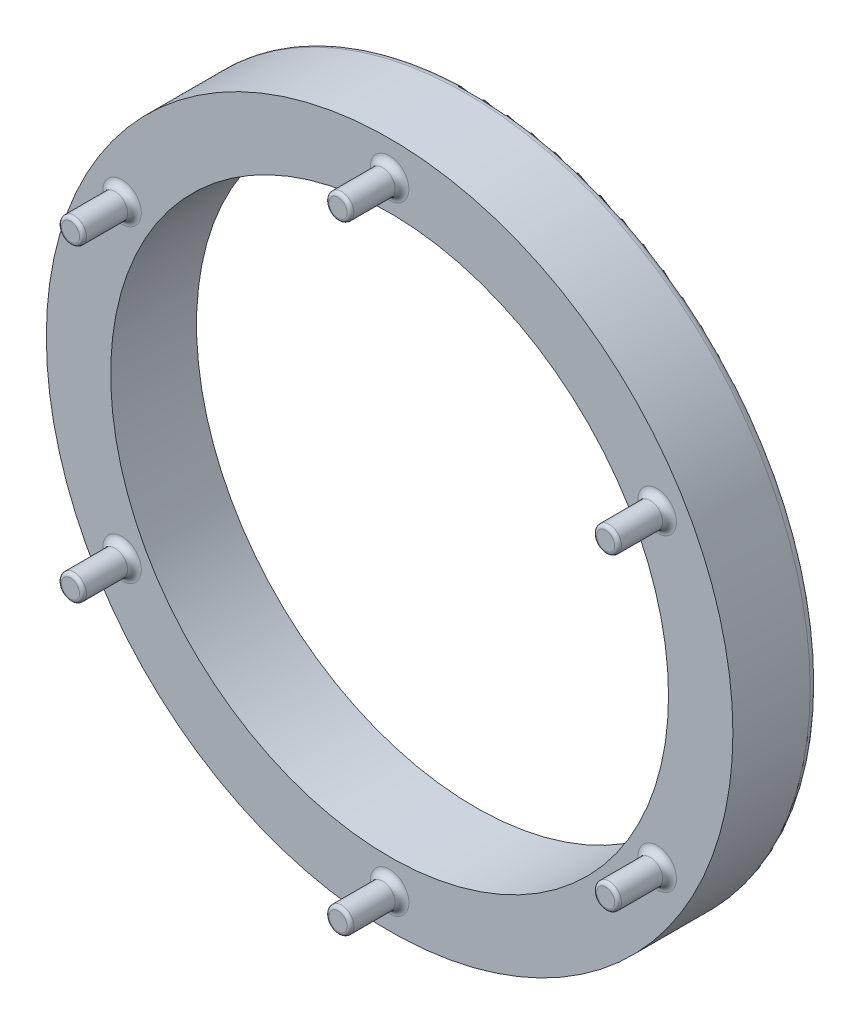
SolidWorks part; units mm, degrees
ref_plane "Front Plane" through (0, 0, 0) normal (0, 0, 1) x (1, 0, 0)
ref_plane "Top Plane" through (0, 0, 0) normal (0, 1, 0) x (1, 0, 0)
ref_plane "Right Plane" through (0, 0, 0) normal (1, 0, 0) x (0, 0, -1)
sketch "Sketch1" plane through (0, 0, 0) normal (0, 0, 1) x (1, 0, 0)
  circle A0 centre (0, 0) radius 20
  dimension "D1" = 40
extrude "Boss-Extrude1" add sketch "Sketch1" along normal blind 5
sketch "Sketch2" plane through (0, 0, 5) normal (0, 0, 1) x (1, 0, 0)
  circle A0 centre (0, 0) radius 18
  dimension "D1" = 36
sketch "Sketch3" plane through (0, 0, 5) normal (0, 0, 1) x (1, 0, 0)
  circle A0 centre (0, 18) radius 0.725
  circle A1 centre (0, 0) radius 18 construction
  circle A2 centre (15.5885, 9) radius 0.725
  circle A3 centre (15.5885, -9) radius 0.725
  circle A4 centre (0, -18) radius 0.725
  circle A5 centre (-15.5885, -9) radius 0.725
  circle A6 centre (-15.5885, 9) radius 0.725
  point P16 (0, 0)
  dimension "D1" = 1.45
  dimension "D2" = 6
extrude "Boss-Extrude3" add sketch "Sketch3" along normal blind 3
fillet "Fillet1" radius 0.4 6 edges at (-14.8635, -9, 5) (0.725, -18, 5) (16.3135, -9, 5) (16.3135, 9, 5) (0.725, 18, 5) (-14.8635, 9, 5)
sketch "Sketch4" plane through (0, 0, 0) normal (0, 0, -1) x (-1, 0, 0)
  circle A0 centre (0, 0) radius 8.5
  dimension "D1" = 17
extrude "Cut-Extrude2" cut sketch "Sketch4" against normal blind 1.5
sketch "Sketch6" plane through (0, 0, 1.5) normal (0, 0, -1) x (-1, 0, 0)
  circle A0 centre (0, 0) radius 5
  dimension "D1" = 10
extrude "Boss-Extrude4" add sketch "Sketch6" along normal blind 0.5
sketch "Sketch7" plane through (0, 0, 1) normal (0, 0, -1) x (-1, 0, 0)
  circle A0 centre (0, 0) radius 4
  dimension "D1" = 8
extrude "Boss-Extrude6" add sketch "Sketch7" along normal blind 4.5
fillet "Fillet2" radius 0.5 1 edges at (20, 0, 0)
fillet "Fillet3" radius 0.5 1 edges at (-8.5, 0, 0)
fillet "Fillet4" radius 0.5 1 edges at (-4, 0, -3.5)
fillet "Fillet5" radius 0.2 6 edges at (0.725, 18, 8) (-14.8635, 9, 8) (-14.8635, -9, 8) (16.3135, -9, 8) (0.725, -18, 8) (16.3135, 9, 8)
sketch "Sketch8" plane through (0, 0, 5) normal (0, 0, 1) x (1, 0, 0)
  circle A0 centre (0, 0) radius 16.25
  dimension "D1" = 32.5
extrude "Cut-Extrude4" cut sketch "Sketch8" against normal blind 1
fillet "Fillet6" radius 0.2 1 edges at (16.25, 0, 4)
sketch "Sketch9" plane through (0, 0, 4) normal (0, 0, 1) x (1, 0, 0)
  circle A0 centre (0, 0) radius 16.25
extrude "Cut-Extrude5" cut sketch "Sketch9" against normal through all and the other way through all
